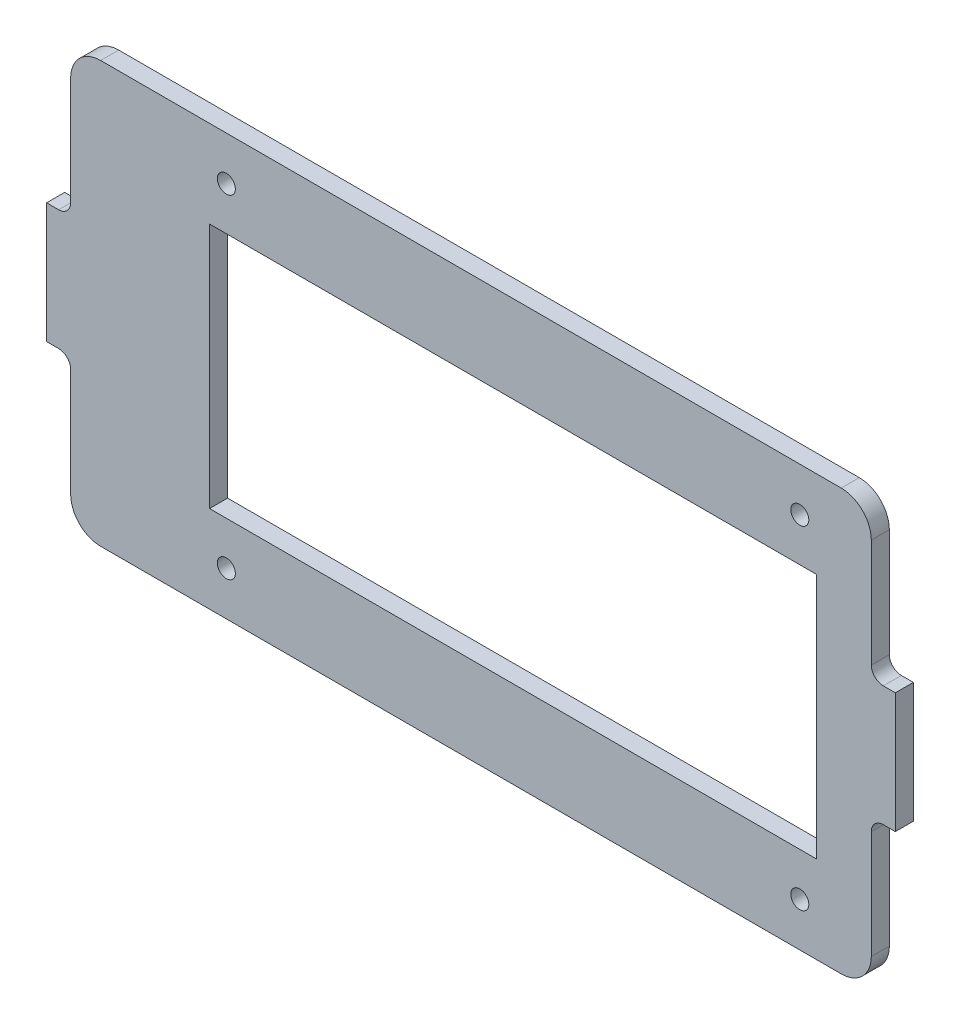
SolidWorks part; units mm, degrees
ref_plane "Plan de face" through (0, 0, 0) normal (0, 0, 1) x (1, 0, 0)
ref_plane "Plan de dessus" through (0, 0, 0) normal (0, 1, 0) x (1, 0, 0)
ref_plane "Plan de droite" through (0, 0, 0) normal (1, 0, 0) x (0, 0, -1)
sketch "Esquisse1" plane through (0, 0, 0) normal (0, 0, 1) x (1, 0, 0)
  line L0 (66.6, 30) -> (66.6, 12)
  line L1 (-61.6, 35) -> (61.6, 35)
  line L2 (0, 27.5291) -> (0, -44.0959) construction
  line L3 (-61.6, -35) -> (61.6, -35)
  line L4 (68.6, 10) -> (70.6, 10)
  line L5 (-43.5, 20.5) -> (57.5, 20.5)
  line L6 (-43.5, 20.5) -> (-43.5, -20.5)
  line L7 (-43.5, -20.5) -> (57.5, -20.5)
  line L8 (57.5, 20.5) -> (57.5, -20.5)
  line L9 (70.6, 10) -> (70.6, -10)
  line L10 (70.6, 0) -> (57.5, 0) construction
  line L11 (68.6, -10) -> (70.6, -10)
  line L12 (66.6, -30) -> (66.6, -12)
  line L14 (-66.6, -30) -> (-66.6, -12)
  line L15 (-68.6, -10) -> (-70.6, -10)
  line L16 (-70.6, 10) -> (-70.6, -10)
  line L17 (-68.6, 10) -> (-70.6, 10)
  line L18 (-66.6, 30) -> (-66.6, 12)
  arc A0 (-61.6, 35) -> (-66.6, 30) centre (-61.6, 30) ccw
  arc A1 (-66.6, -30) -> (-61.6, -35) centre (-61.6, -30) ccw
  arc A2 (61.6, -35) -> (66.6, -30) centre (61.6, -30) ccw
  arc A3 (61.6, 35) -> (66.6, 30) centre (61.6, 30) cw
  arc A4 (68.6, 10) -> (66.6, 12) centre (68.6, 12) cw
  arc A5 (68.6, -10) -> (66.6, -12) centre (68.6, -12) ccw
  arc A6 (-68.6, -10) -> (-66.6, -12) centre (-68.6, -12) cw
  arc A7 (-68.6, 10) -> (-66.6, 12) centre (-68.6, 12) ccw
  point P11 (-67.5, 35)
  point P16 (52.5, -35)
  point P40 (0, 0)
  dimension "D9" = 5
  dimension "D8" = 2
  dimension "D3" = 101
  dimension "D4" = 41
  dimension "D5" = 20.5
  dimension "D6" = 35
  dimension "D7" = 66.6
  dimension "D10" = 10
  dimension "D11" = 4
extrude "Boss.-Extru.1" add sketch "Esquisse1" along normal blind 3
hole_wizard "Diamètre du perçage Ø3.0 (3)1" positions "Esquisse4" profile "Esquisse5" hole size "Ø3.0" standard "Ansi Metric" end condition up to next
sketch "Esquisse4" plane through (0, 0, 3) normal (0, 0, 1) x (1, 0, 0)
  point P0 (-40.7, 27.7)
  point P3 (-40.7, -27.7)
  point P6 (54.7, -27.7)
  point P9 (54.7, 27.7)
sketch "Esquisse5" plane through (-40.7, 27.7, 3) normal (1, 0, 0) x (0, -1, 0)
  line L0 (0, 0) -> (0, 3)
  line L1 (0, 3) -> (1.5, 3)
  line L2 (1.5, 3) -> (1.5, 0)
  line L5 (1.5, 0) -> (0, 0)
  line L11 (0, -6.35) -> (0, 107.95) construction
  dimension "Diamètre du perçage jusqu'au prochain" = 3
  dimension "Profondeur du perçage jusqu'au prochain" = 3
